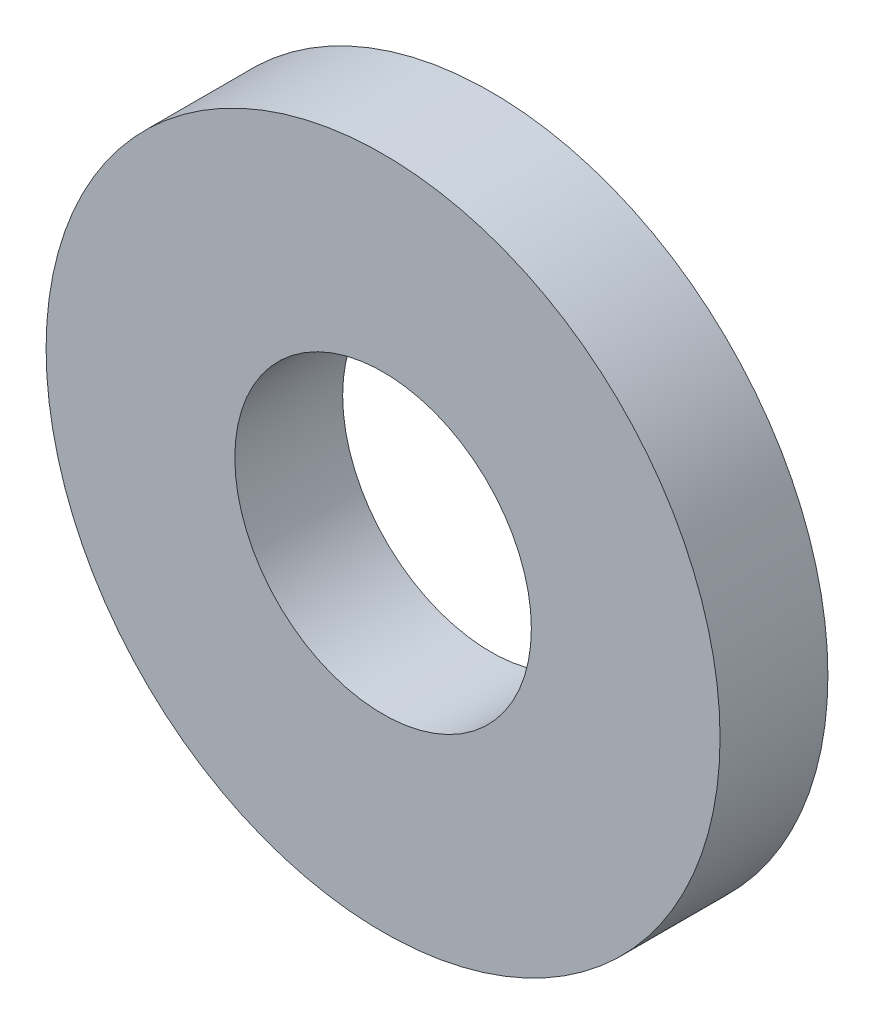
SolidWorks part; units mm, degrees
ref_plane "Front Plane" through (0, 0, 0) normal (0, 0, 1) x (1, 0, 0)
ref_plane "Top Plane" through (0, 0, 0) normal (0, 1, 0) x (1, 0, 0)
ref_plane "Right Plane" through (0, 0, 0) normal (1, 0, 0) x (0, 0, -1)
sketch "Sketch1" plane through (0, 0, 0) normal (0, 0, 1) x (1, 0, 0)
  circle A0 centre (0, 0) radius 2.5 construction
  circle A1 centre (0, 0) radius 1.1 construction
  point P5 (-1.1, 0)
  point P6 (1.1, 0)
  point P7 (2.5, 0)
  point P8 (-2.5, 0)
  dimension "OD" = 5
  dimension "ID" = 2.2
sketch "Sketch2" plane through (0, 0, 0) normal (1, 0, 0) x (0, 0, -1)
  line L0 (0.4, 0) -> (-0.4, 0) construction
  line L1 (0, 2.5) -> (0, -2.5) construction
  line L2 (0, 2.5) -> (0, -2.5) construction
  line L3 (0.4, 2.5) -> (-0.4, 2.5) construction
  line L4 (0.4, -2.5) -> (-0.4, -2.5) construction
  line L5 (-0.4, -2.5) -> (-0.4, 2.5) construction
  line L6 (0.4, -2.5) -> (0.4, 2.5) construction
  point P4 (0, 0)
  point P10 (0, 2.5)
  point P11 (-0.4, 2.5)
  point P14 (0, -2.5)
  point P15 (-0.4, -2.5)
  point P16 (0.4, -2.5)
  point P17 (0.4, 2.5)
  point P18 (0.4, 0)
  point P19 (-0.4, 0)
  dimension "Thickness" = 0.8
sketch "Sketch3" plane through (0, 0, 0) normal (0, 0, 1) x (1, 0, 0)
  circle A0 centre (0, 0) radius 2.5 construction
  circle A1 centre (0, 0) radius 1.1 construction
  circle A2 centre (0, 0) radius 2.5
  circle A3 centre (0, 0) radius 1.1
extrude "Boss-Extrude1" add sketch "Sketch3" along normal mid plane 0.8
equation "\"D1@Boss-Extrude1\"=\"Thickness@Sketch2\""
